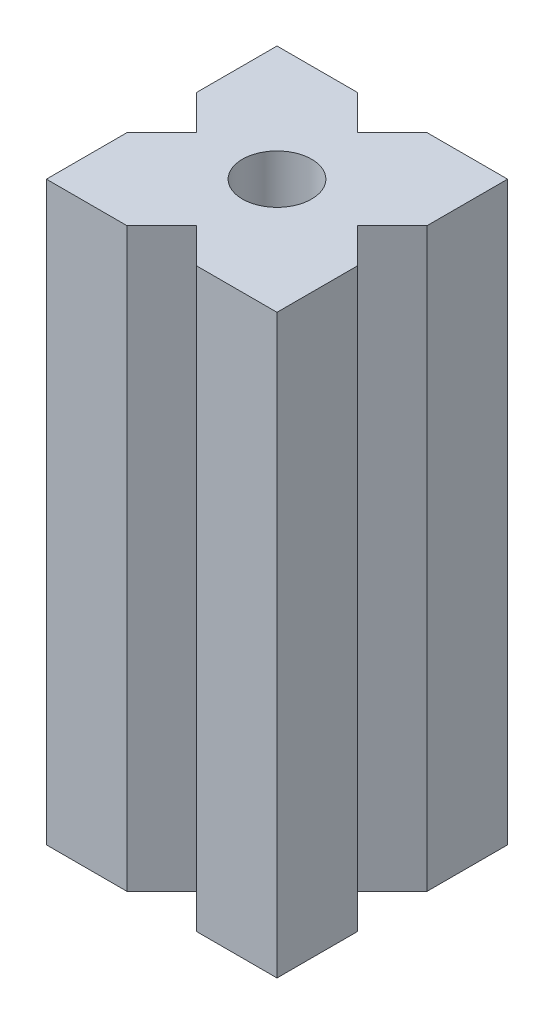
SolidWorks part; units mm, degrees
ref_plane "Front" through (0, 0, 0) normal (0, 0, 1) x (1, 0, 0)
ref_plane "Top" through (0, 0, 0) normal (0, 1, 0) x (1, 0, 0)
ref_plane "Right" through (0, 0, 0) normal (1, 0, 0) x (0, 0, -1)
sketch "Skizze1" plane through (0, 0, 0) normal (0, 1, 0) x (1, 0, 0)
  line L0 (0, 0) -> (0, 10) construction
  line L1 (-10, -10) -> (10, -10)
  line L2 (-10, -10) -> (-10, 10)
  line L3 (-10, 10) -> (10, 10)
  line L4 (10, -10) -> (10, 10)
  line L5 (0, 0) -> (10, 0) construction
  dimension "D1" = 20
extrude "Aufsatz-Linear austragen1" add sketch "Skizze1" along normal mid plane 50
sketch "Skizze2" plane through (0, 25, 0) normal (0, 1, 0) x (1, 0, 0)
  line L0 (0, 10) -> (0, -10) construction
  line L1 (-10, 0) -> (10, 0) construction
  line L2 (-3, 10) -> (0, 7)
  line L3 (3, 10) -> (0, 7)
  line L4 (0, 0) -> (10, 10) construction
  line L5 (-3, 10) -> (3, 10)
  line L6 (10, 3) -> (7, 0)
  line L7 (10, -3) -> (7, 0)
  line L8 (10, -3) -> (10, 3)
  line L9 (-10, -3) -> (-10, 3)
  line L10 (-10, -3) -> (-7, 0)
  line L11 (-10, 3) -> (-7, 0)
  line L12 (-3, -10) -> (3, -10)
  line L13 (3, -10) -> (0, -7)
  line L14 (-3, -10) -> (0, -7)
  line L15 (10, 10) -> (-10, 10) construction
  line L16 (10, -10) -> (10, 10) construction
  line L17 (-10, -10) -> (10, -10) construction
  dimension "D1" = 3
  dimension "D2" = 3
extrude "Schnitt-Linear austragen1" cut sketch "Skizze2" against normal through all
ref_plane "Ebene1" [suppressed] through (0, 0, 0) normal (1, 0, 0) x (0, 0, -1)
sketch "Skizze3" plane through (0, 25, 0) normal (0, 1, 0) x (1, 0, 0)
  line L0 (-7, 0) -> (7, 0) construction
  circle A0 centre (0, 0) radius 3
  dimension "D1" = 6
extrude "Schnitt-Linear austragen2" cut sketch "Skizze3" against normal through all
ref_plane "Plane1" [suppressed] through (0, 0, 0) normal (0, 1, 0) x (1, 0, 0)
sketch "Sketch1" [suppressed] plane through (0, 0, 10) normal (0, 0, 1) x (1, 0, 0)
  circle A0 centre (0, -4.6) radius 3
  dimension "D1" = 6
extrude "Cut-Extrude1" [suppressed] cut sketch "Sketch1" against normal through all
